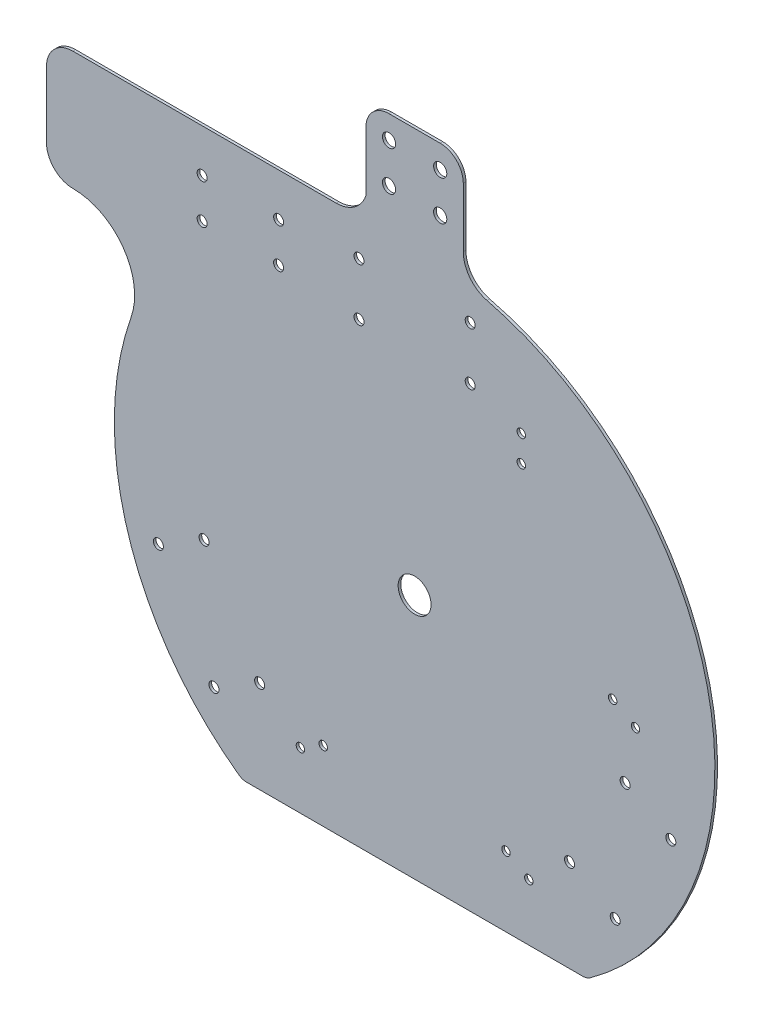
SolidWorks part; units mm, degrees
ref_plane "Front Plane" through (0, 0, 0) normal (0, 0, 1) x (1, 0, 0)
ref_plane "Top Plane" through (0, 0, 0) normal (0, 1, 0) x (1, 0, 0)
ref_plane "Right Plane" through (0, 0, 0) normal (1, 0, 0) x (0, 0, -1)
sketch "Sketch1" plane through (0, 0, 0) normal (0, 0, 1) x (1, 0, 0)
  line L0 (0, 3.3041) -> (-164.5412, 3.3041)
  line L1 (-177.2412, -9.3959) -> (-177.2412, -41.275)
  line L3 (-82.9336, -259.7305) -> (82.9336, -259.7305)
  line L4 (-164.5412, -53.975) -> (-115.253, -53.975) construction
  line L5 (-52.5707, -47.625) -> (-109.7207, -47.625) construction
  line L6 (-23.4315, 3.3041) -> (23.4315, 3.3041) construction
  line L7 (-23.4315, 3.3041) -> (-23.4315, 53.34)
  line L8 (-23.4315, 53.34) -> (23.4315, 53.34)
  line L9 (23.4315, 3.3041) -> (23.4315, 53.34)
  arc A0 (-136.4766, -93.5291) -> (0, 3.3041) centre (0, -141.2875) ccw
  arc A2 (-164.5412, -53.975) -> (-177.2412, -41.275) centre (-164.5412, -41.275) cw
  arc A3 (-164.5412, 3.3041) -> (-177.2412, -9.3959) centre (-164.5412, -9.3959) ccw
  arc A4 (-164.5412, -53.975) -> (-136.4766, -93.5291) centre (-164.5412, -83.7083) cw
  arc A5 (0, 3.3041) -> (-136.4766, -93.5291) centre (0, -141.2875) ccw construction
  circle A6 centre (-101.3708, -168.9081) radius 2.413 construction
  circle A7 centre (-123.3679, -181.6081) radius 2.413 construction
  circle A8 centre (-96.6026, -227.9669) radius 2.413 construction
  circle A9 centre (-74.6056, -215.2669) radius 2.413 construction
  circle A10 centre (-54.9884, -232.3538) radius 2.032 construction
  circle A11 centre (-43.9899, -226.0038) radius 2.032 construction
  circle A12 centre (43.9899, -226.0038) radius 2.032 construction
  circle A13 centre (54.9884, -232.3538) radius 2.032 construction
  circle A14 centre (96.6026, -227.9669) radius 2.413 construction
  circle A15 centre (74.6056, -215.2669) radius 2.413 construction
  circle A16 centre (123.3679, -181.6081) radius 2.413 construction
  circle A17 centre (101.3708, -168.9081) radius 2.413 construction
  circle A18 centre (95.3614, -137.0257) radius 2.032 construction
  circle A19 centre (106.3599, -143.3757) radius 2.032 construction
  circle A20 centre (51.3715, -60.833) radius 2.032 construction
  circle A21 centre (51.3715, -48.133) radius 2.032 construction
  circle A22 centre (26.7652, -39.6875) radius 2.413 construction
  circle A23 centre (26.7652, -14.2875) radius 2.413 construction
  circle A24 centre (-26.7652, -14.2875) radius 2.413 construction
  circle A25 centre (-26.7652, -39.6875) radius 2.413 construction
  circle A26 centre (-65.4812, -36.5125) radius 2.413 construction
  circle A29 centre (-65.4812, -17.4625) radius 2.413 construction
  circle A30 centre (-101.3708, -168.9081) radius 2.413
  circle A31 centre (-123.3679, -181.6081) radius 2.413
  circle A32 centre (-96.6026, -227.9669) radius 2.413
  circle A33 centre (-74.6056, -215.2669) radius 2.413
  circle A34 centre (-54.9884, -232.3538) radius 2.032
  circle A35 centre (-43.9899, -226.0038) radius 2.032
  circle A36 centre (43.9899, -226.0038) radius 2.032
  circle A37 centre (54.9884, -232.3538) radius 2.032
  circle A38 centre (96.6026, -227.9669) radius 2.413
  circle A39 centre (74.6056, -215.2669) radius 2.413
  circle A40 centre (123.3679, -181.6081) radius 2.413
  circle A41 centre (101.3708, -168.9081) radius 2.413
  circle A42 centre (95.3614, -137.0257) radius 2.032
  circle A43 centre (106.3599, -143.3757) radius 2.032
  circle A44 centre (51.3715, -60.833) radius 2.032
  circle A45 centre (51.3715, -48.133) radius 2.032
  circle A46 centre (26.7652, -39.6875) radius 2.413
  circle A47 centre (26.7652, -14.2875) radius 2.413
  circle A48 centre (-26.7652, -14.2875) radius 2.413
  circle A49 centre (-26.7652, -39.6875) radius 2.413
  circle A50 centre (-65.4812, -36.5125) radius 2.413
  circle A53 centre (-65.4812, -17.4625) radius 2.413
  circle A54 centre (0, -141.2875) radius 7.9375
  circle A55 centre (-12.319, 23.1775) radius 3.175
  circle A56 centre (12.319, 23.1775) radius 3.175
  circle A57 centre (12.319, 42.2275) radius 3.175
  circle A58 centre (-12.319, 42.2275) radius 3.175
  arc A59 (23.4315, 13.6525) -> (34.8588, -0.9607) centre (38.4889, 13.6525) ccw
  arc A60 (-23.4315, 13.6525) -> (-37.7336, 3.3041) centre (-37.7336, 18.3615) cw
  arc A61 (-12.319, 53.34) -> (-23.4315, 42.2275) centre (-12.319, 42.2275) ccw
  arc A62 (12.319, 53.34) -> (23.4315, 42.2275) centre (12.319, 42.2275) cw
  arc A63 (-76.5316, -258.5399) -> (-75.4473, -258.8304) centre (-75.8442, -258.143) ccw construction
  point P95 (0, 53.34)
  dimension "D1" = 6.35
  dimension "D3" = 12.7
  dimension "D4" = 15.875
  dimension "D5" = 19.05
  dimension "D7" = 6.35
  dimension "D12" = 9.525
  dimension "D2" = 6.35
  dimension "D6" = 12.319
  dimension "D8" = 1.5875
  dimension "D9" = 164.465
  dimension "D11" = 11.1125
extrude "Boss-Extrude1" add sketch "Sketch1" along normal blind 1.27
sketch "Sketch2" plane through (0, 0, 1.27) normal (0, 0, 1) x (1, 0, 0)
  line L0 (-107.3912, -36.5125) -> (-102.3112, -36.5125) construction
  line L1 (-107.3912, -34.0995) -> (-102.3112, -34.0995) construction
  line L2 (-107.3912, -38.9255) -> (-102.3112, -38.9255) construction
  line L3 (-107.3912, -17.4625) -> (-102.3112, -17.4625) construction
  line L4 (-107.3912, -15.0495) -> (-102.3112, -15.0495) construction
  line L5 (-107.3912, -19.8755) -> (-102.3112, -19.8755) construction
  arc A0 (-107.3912, -34.0995) -> (-107.3912, -38.9255) centre (-107.3912, -36.5125) ccw construction
  arc A1 (-102.3112, -38.9255) -> (-102.3112, -34.0995) centre (-102.3112, -36.5125) ccw construction
  circle A2 centre (-102.3112, -17.4625) radius 2.413
  circle A3 centre (-102.3112, -36.5125) radius 2.413
  arc A4 (-107.3912, -15.0495) -> (-107.3912, -19.8755) centre (-107.3912, -17.4625) ccw construction
  arc A5 (-102.3112, -19.8755) -> (-102.3112, -15.0495) centre (-102.3112, -17.4625) ccw construction
  circle A7 centre (-65.4812, -17.4625) radius 2.413 construction
  point P2 (-104.8512, -36.5125)
  point P8 (-104.8512, -17.4625)
  point P9 (-95.2316, -36.5125)
  point P16 (-104.8512, -17.4625)
  point P22 (-65.4812, -36.5125)
  point P25 (-65.4812, -17.4625)
  dimension "D2" = 36.83
  dimension "D3" = 5.08
  dimension "D1" = 5.08
extrude "Cut-Extrude1" cut sketch "Sketch2" against normal through all
fillet "Fillet1" radius 6.35 2 edges at (82.9336, -259.7305, 0.635) (-82.9336, -259.7305, 0.635)
equation "\"Thick\"= \"in\""
